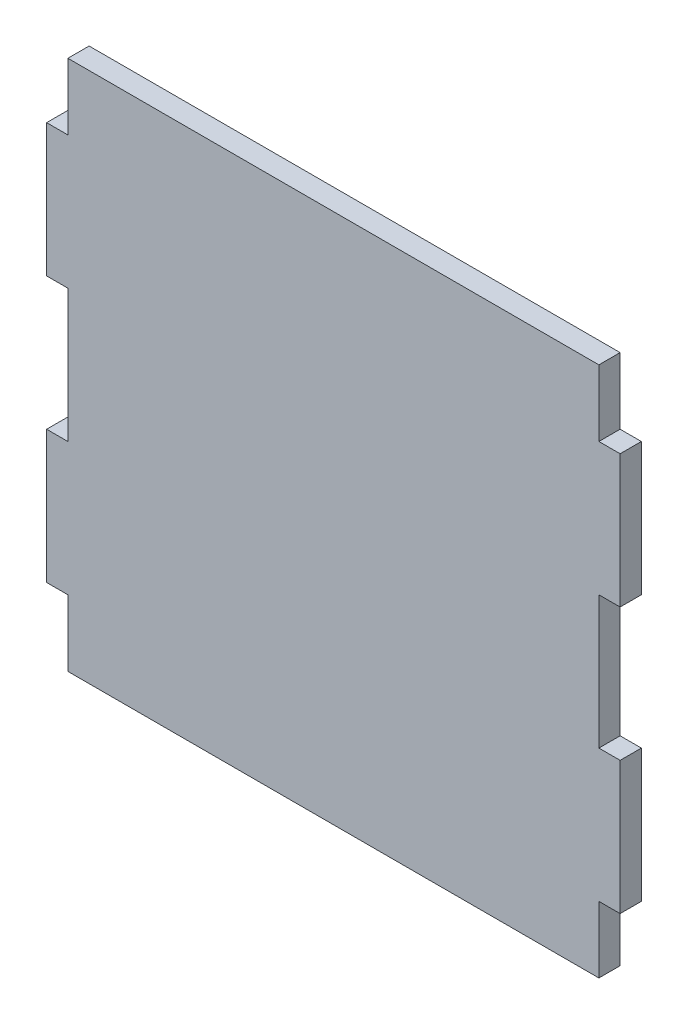
SolidWorks part; units mm, degrees
ref_plane "Front Plane" through (0, 0, 0) normal (0, 0, 1) x (1, 0, 0)
ref_plane "Top Plane" through (0, 0, 0) normal (0, 1, 0) x (1, 0, 0)
ref_plane "Right Plane" through (0, 0, 0) normal (1, 0, 0) x (0, 0, -1)
sketch "Sketch1" plane through (0, 0, 0) normal (0, 0, 1) x (1, 0, 0)
  line L0 (50, 0) -> (50, -100) construction
  line L1 (0, 0) -> (100, 0)
  line L2 (0, 0) -> (0, -12.5)
  line L3 (0, -100) -> (100, -100)
  line L5 (0, -12.5) -> (-4, -12.5)
  line L6 (0, -87.5) -> (0, -100)
  line L7 (0, -37.5) -> (-4, -37.5)
  line L8 (-4, -12.5) -> (-4, -37.5)
  line L9 (0, -62.5) -> (-4, -62.5)
  line L10 (100, -37.5) -> (100, -62.5)
  line L11 (0, -87.5) -> (-4, -87.5)
  line L12 (-4, -62.5) -> (-4, -87.5)
  line L13 (0, -37.5) -> (0, -62.5)
  line L14 (104, -62.5) -> (104, -87.5)
  line L15 (100, -87.5) -> (104, -87.5)
  line L16 (100, -62.5) -> (104, -62.5)
  line L17 (104, -12.5) -> (104, -37.5)
  line L18 (100, -37.5) -> (104, -37.5)
  line L19 (100, -87.5) -> (100, -100)
  line L20 (100, -12.5) -> (104, -12.5)
  line L21 (100, 0) -> (100, -12.5)
  dimension "D1" = 12.5
  dimension "D2" = 25
  dimension "D3" = 12.5
  dimension "D4" = 25
  dimension "D5" = 100
  dimension "D6" = 100
  dimension "D7" = 4
  dimension "D8" = 4
extrude "Boss-Extrude1" add sketch "Sketch1" along normal blind 4
